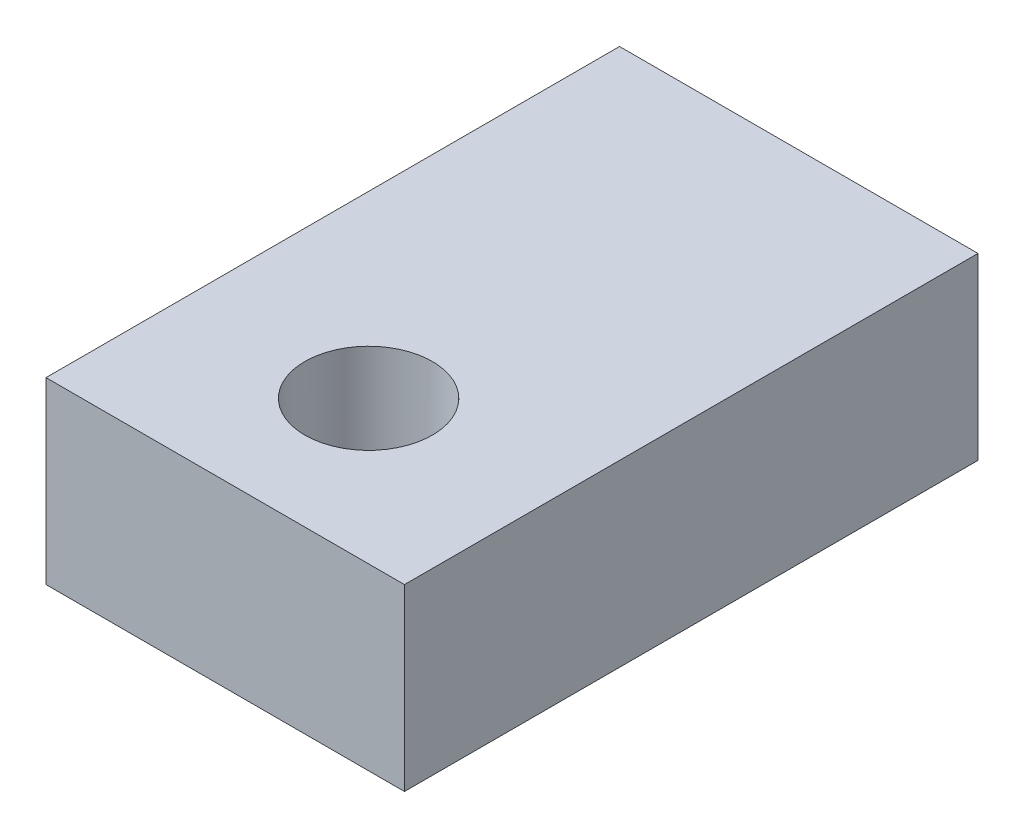
SolidWorks part; units mm, degrees
ref_plane "Front Plane" through (0, 0, 0) normal (0, 0, 1) x (1, 0, 0)
ref_plane "Top Plane" through (0, 0, 0) normal (0, 1, 0) x (1, 0, 0)
ref_plane "Right Plane" through (0, 0, 0) normal (1, 0, 0) x (0, 0, -1)
sketch "Sketch1" plane through (0, 0, 0) normal (0, 1, 0) x (1, 0, 0)
  line L1 (-3.175, -5.08) -> (3.175, -5.08)
  line L2 (-3.175, -5.08) -> (-3.175, 5.08)
  line L3 (-3.175, 5.08) -> (3.175, 5.08)
  line L4 (3.175, -5.08) -> (3.175, 5.08)
  line L5 (-3.175, -5.08) -> (3.175, 5.08) construction
  line L6 (-3.175, 5.08) -> (3.175, -5.08) construction
  point P0 (0, 0)
  dimension "D1" = 6.35
  dimension "D2" = 10.16
extrude "Boss-Extrude1" add sketch "Sketch1" along normal blind 3.175
hole_wizard "#4-40 Tapped Hole1" positions "Sketch2" profile "Sketch3" tap size "#4-40" standard "ANSI Inch"
sketch "Sketch2" plane through (0, 3.175, 0) normal (0, 1, 0) x (1, 0, 0)
  line L0 (-3.175, -5.08) -> (3.175, -5.08) construction
  point P0 (0, -2.54)
  dimension "D1" = 2.54
sketch "Sketch3" plane through (0, 3.175, 2.54) normal (1, 0, 0) x (0, 0, 1)
  line L0 (0, 0) -> (0, 8.2738)
  line L1 (0, 8.2738) -> (1.1303, 7.5946)
  line L2 (1.1303, 7.5946) -> (1.1303, 0)
  line L5 (1.1303, 0) -> (0, 0)
  line L10 (0, 8.2738) -> (-1.1303, 7.5946) construction
  line L11 (0, -6.35) -> (0, 107.95) construction
  dimension "Tap Drill Dia." = 2.2606
  dimension "Tap Drill Depth" = 7.5946
  dimension "Drill Angle" = 118
cosmetic thread "Hole Thread1"
